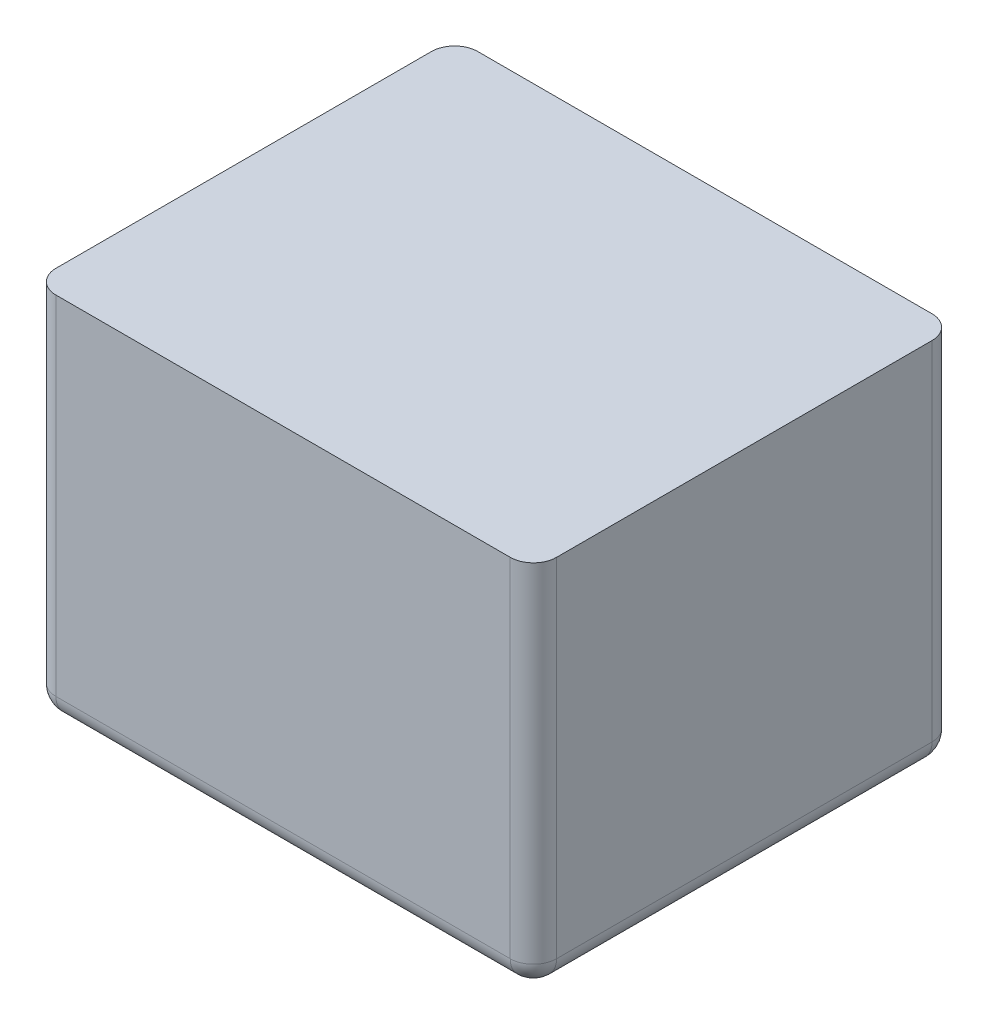
SolidWorks part; units mm, degrees
ref_plane "Ebene vorne" through (0, 0, 0) normal (0, 0, 1) x (1, 0, 0)
ref_plane "Ebene oben" through (0, 0, 0) normal (0, 1, 0) x (1, 0, 0)
ref_plane "Ebene rechts" through (0, 0, 0) normal (1, 0, 0) x (0, 0, -1)
sketch "Skizze1" plane through (0, 0, 0) normal (0, 1, 0) x (1, 0, 0)
  line L1 (-16.2, -13.65) -> (16.2, -13.65)
  line L2 (-16.2, -13.65) -> (-16.2, 13.65)
  line L3 (-16.2, 13.65) -> (16.2, 13.65)
  line L4 (16.2, -13.65) -> (16.2, 13.65)
  line L5 (-16.2, -13.65) -> (16.2, 13.65) construction
  line L6 (-16.2, 13.65) -> (16.2, -13.65) construction
  point P0 (0, 0)
  dimension "D1" = 27.3
  dimension "D2" = 32.4
extrude "Aufsatz-Linear austragen1" add sketch "Skizze1" along normal blind 24
fillet "Verrundung1" radius 1.5 8 edges at (16.2, 12, -13.65) (-16.2, 12, -13.65) (-16.2, 12, 13.65) (16.2, 12, 13.65) (0, 0, -13.65) (-16.2, 0, 0) (0, 0, 13.65) (16.2, 0, 0)
